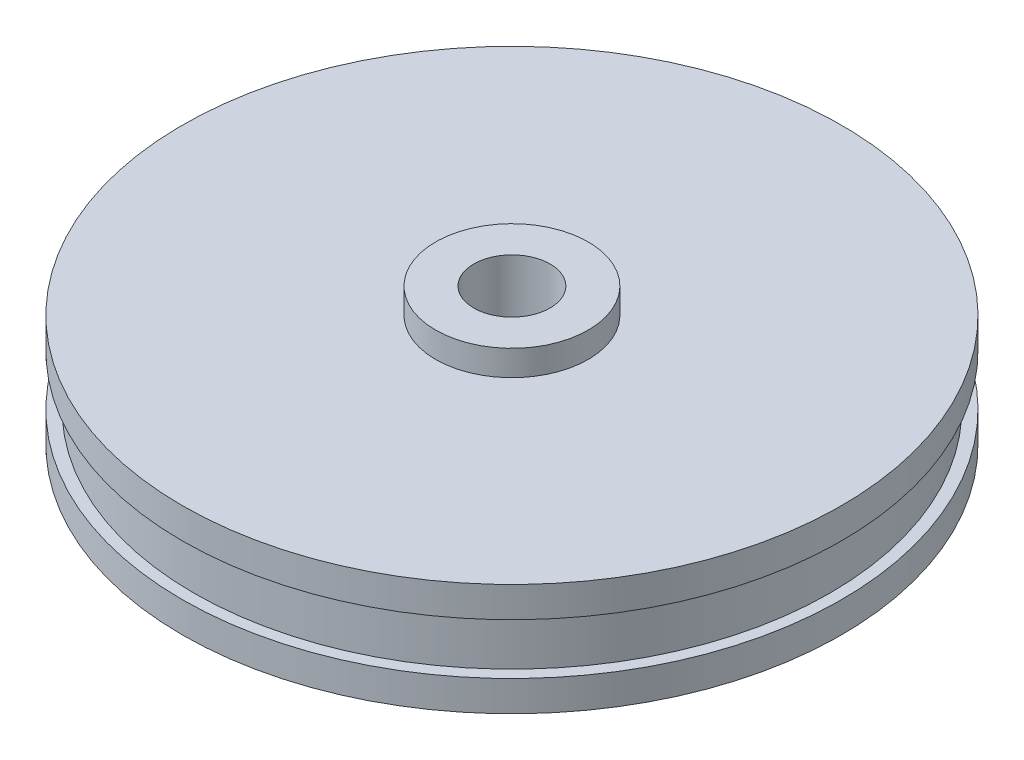
SolidWorks part; units mm, degrees
ref_plane "Plan de face" through (0, 0, 0) normal (0, 0, 1) x (1, 0, 0)
ref_plane "Plan de dessus" through (0, 0, 0) normal (0, 1, 0) x (1, 0, 0)
ref_plane "Plan de droite" through (0, 0, 0) normal (1, 0, 0) x (0, 0, -1)
ref_axis "Axe2" through (0, 17.85, 0) along (0, -1, 0)
sketch "Esquisse1" plane through (0, 0, 0) normal (0, 0, 1) x (1, 0, 0)
  line L0 (12.95, -2.2) -> (1.5, -2.2)
  line L1 (1.5, -2.2) -> (1.5, 3.2)
  line L2 (1.5, 3.2) -> (3, 3.2)
  line L3 (3, 3.2) -> (3, 2.2)
  line L4 (3, 2.2) -> (12.95, 2.2)
  line L5 (12.95, 2.2) -> (12.95, 1)
  line L6 (12.95, 1) -> (12.5, 1)
  line L7 (12.5, 1) -> (12.5, -1)
  line L8 (12.5, -1) -> (12.95, -1)
  line L9 (12.95, -1) -> (12.95, -2.2)
  line L10 (0, -2.97) -> (0, 2.97) construction
  line L12 (14.245, 0) -> (-14.245, 0) construction
  point P2 (12.5, 0)
  dimension "D1" = 12.5
  dimension "D2" = 1
  dimension "D3" = 2
  dimension "D4" = 0.45
  dimension "D5" = 1.2
  dimension "D6" = 1.5
  dimension "D7" = 3
revolve "Révolution2" add sketch "Esquisse1" angle 360 about axis through (0, 17.85, 0) along (0, -1, 0)
